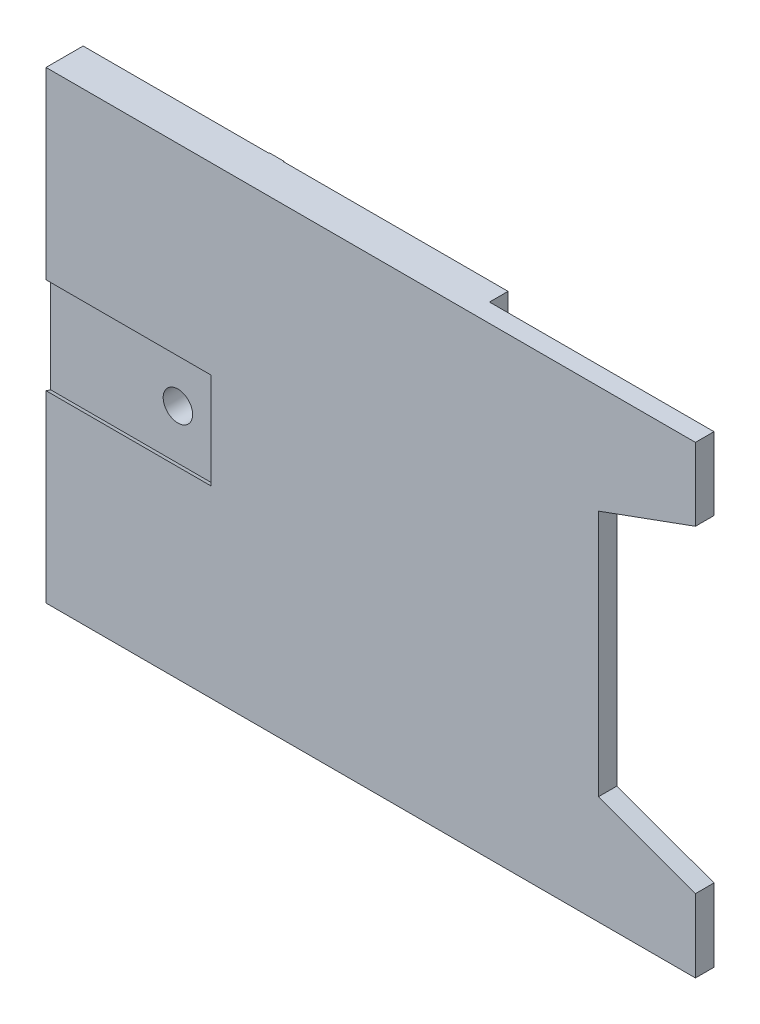
SolidWorks part; units mm, degrees
ref_plane "Front Plane" through (0, 0, 0) normal (0, 0, 1) x (1, 0, 0)
ref_plane "Top Plane" through (0, 0, 0) normal (0, 1, 0) x (1, 0, 0)
ref_plane "Right Plane" through (0, 0, 0) normal (1, 0, 0) x (0, 0, -1)
sketch "Sketch2" plane through (0, 0, 0) normal (0, 0, 1) x (1, 0, 0)
  line L0 (50, 42.164) -> (50, 50)
  line L1 (0, 0) -> (50, 0)
  line L2 (0, 0) -> (0, 47.46)
  line L3 (1.606, 50) -> (50, 50)
  line L4 (50, 0) -> (50, 7.874)
  line L5 (39.536, 38.354) -> (39.536, 11.684)
  line L6 (39.536, 38.354) -> (50, 42.164)
  line L7 (39.536, 11.684) -> (50, 7.874)
  line L27 (0, 47.46) -> (1.606, 47.46)
  line L28 (1.606, 47.46) -> (1.606, 50)
extrude "Boss-Extrude1" add sketch "Sketch2" along normal blind 4
ref_plane "Plane1" through (0, 50, 0) normal (0, 1, 0) x (1, 0, 0)
sketch "Sketch3" plane through (0, 50, 0) normal (0, 1, 0) x (1, 0, 0)
  line L0 (25.803, 0) -> (25.803, -4) construction
  line L3 (25.803, 0) -> (25.803, -2)
  line L4 (25.803, -2) -> (50, -2)
  line L6 (50, -2) -> (50, 0)
  line L7 (50, 0) -> (25.803, 0)
extrude "Cut-Extrude1" cut sketch "Sketch3" against normal through all
ref_plane "Plane2" through (0, 0, 0) normal (-1, 0, 0) x (0, 0, 1)
sketch "Sketch5" plane through (0, 0, 0) normal (-1, 0, 0) x (0, 0, 1)
  line L1 (0, 0) -> (4, 0)
  line L2 (0, 0) -> (0, 50)
  line L3 (0, 50) -> (4, 50)
  line L4 (4, 0) -> (4, 50)
extrude "Boss-Extrude2" add sketch "Sketch5" along normal blind 20
ref_plane "Plane3" through (0, 0, 0) normal (0, 0, -1) x (-1, 0, 0)
ref_plane "Plane4" through (-20, 0, 0) normal (-1, 0, 0) x (0, 0, 1)
sketch "Sketch6" plane through (-20, 0, 0) normal (-1, 0, 0) x (0, 0, 1)
  line L0 (4, 25) -> (0, 25) construction
  line L1 (4, 0) -> (4, 50) construction
  line L2 (0, 25.1916) -> (0, -25.1916) construction
  line L3 (2, 25) -> (2, 50) construction
  line L4 (2.2, 50) -> (-2.2, 50) construction
  line L5 (3.5, 19.6566) -> (3.5, 30.3434)
  line L6 (0.5, 19.6566) -> (0.5, 30.3434)
  line L7 (4, 30.177) -> (4, 19.823)
  line L8 (0, 30.177) -> (0, 19.823)
  arc A0 (0, 19.823) -> (0.5, 19.6566) centre (2, 25) ccw
  arc A1 (4, 30.177) -> (3.5, 30.3434) centre (2, 25) ccw
  arc A2 (0.5, 30.3434) -> (0, 30.177) centre (2, 25) ccw
  arc A3 (3.5, 19.6566) -> (4, 19.823) centre (2, 25) ccw
  point P16 (3.5, 25)
  point P17 (0.5, 25)
extrude "Cut-Extrude2" cut sketch "Sketch6" against normal blind 17.78
sketch "Sketch7" plane through (0, 0, 0) normal (0, 0, -1) x (-1, 0, 0)
  line L0 (2.22, 25) -> (6.284, 25) construction
  line L2 (2.22, 30.177) -> (2.22, 19.823) construction
  circle A0 centre (6.284, 25) radius 1.5875
extrude "Cut-Extrude3" cut sketch "Sketch7" against normal through all
sketch "Sketch8" plane through (0, 0, 4) normal (0, 0, 1) x (1, 0, 0)
  line L1 (0, 50) -> (1.606, 50)
  line L2 (0, 50) -> (0, 47.46)
  line L3 (0, 47.46) -> (1.606, 47.46)
  line L4 (1.606, 50) -> (1.606, 47.46)
extrude "Boss-Extrude3" add sketch "Sketch8" against normal blind 4.064
